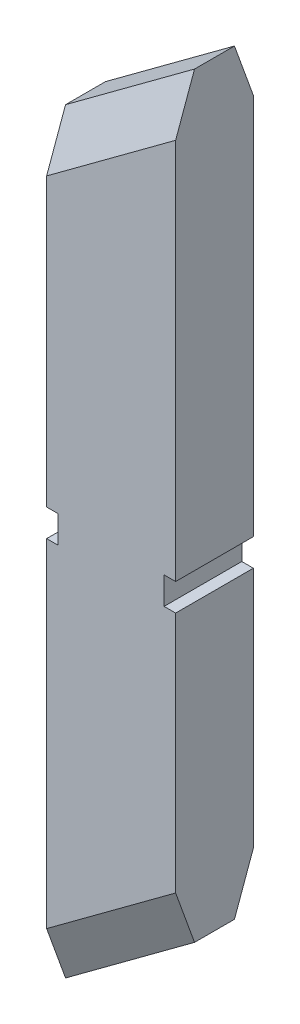
SolidWorks part; units mm, degrees
ref_plane "Front Plane" through (0, 0, 0) normal (0, 0, 1) x (1, 0, 0)
ref_plane "Top Plane" through (0, 0, 0) normal (0, 1, 0) x (1, 0, 0)
ref_plane "Right Plane" through (0, 0, 0) normal (1, 0, 0) x (0, 0, -1)
sketch "Sketch1" plane through (0, 0, 0) normal (0, 0, 1) x (1, 0, 0)
  line L0 (2.9365, 23.3863) -> (2.9365, -12.6137)
  line L1 (2.9365, 23.3863) -> (-3.2035, 18.848)
  line L2 (2.9365, -12.6137) -> (-3.2035, -17.152)
  line L3 (-3.2035, 18.848) -> (-3.2035, -17.152)
  point P0 (-3.2035, 3.528)
  point P5 (-3.2035, 1.958)
  dimension "D1" = 6.14
  dimension "D2" = 36
  dimension "D3" = 15.32
  dimension "D4" = 1.57
extrude "Boss-Extrude1" add sketch "Sketch1" along normal blind 3.7
chamfer "Chamfer1" distance 0.9 distance2 2 1 edges at (-0.1335, 21.1172, 3.7)
chamfer "Chamfer2" distance 2 distance2 0.9 1 edges at (-0.1335, 21.1172, 0)
chamfer "Chamfer4" distance 0.9 distance2 2 1 edges at (-0.1335, -14.8828, 3.7)
chamfer "Chamfer5" distance 2 distance2 0.9 1 edges at (-0.1335, -14.8828, 0)
sketch "Sketch2" plane through (0, 0, 3.7) normal (0, 0, 1) x (1, 0, 0)
  line L0 (-3.2035, 16.361) -> (-3.2035, -14.6649) construction
  line L1 (-3.2035, 2.711) -> (-2.6535, 2.711)
  line L2 (-2.6535, 2.711) -> (-2.6535, 1.411)
  line L3 (-2.6535, 1.411) -> (-3.2035, 1.411)
  point P0 (-3.2035, 2.711)
  point P1 (-3.2035, 1.411)
  dimension "D1" = 13.65
  dimension "D2" = 1.3
  dimension "D3" = 0.55
extrude "Cut-Extrude2" cut sketch "Sketch2" against normal through all and the other way through all flip side to cut
sketch "Sketch3" plane through (0, 0, 3.7) normal (0, 0, 1) x (1, 0, 0)
  line L0 (2.9365, 2.711) -> (2.3865, 2.711)
  line L1 (2.9365, -10.1267) -> (2.9365, 20.8993) construction
  line L2 (2.3865, 2.711) -> (2.3865, 1.411)
  line L3 (2.3865, 1.411) -> (2.9365, 1.411)
  dimension "D1" = 0.55
extrude "Cut-Extrude4" cut sketch "Sketch3" against normal through all and the other way through all
